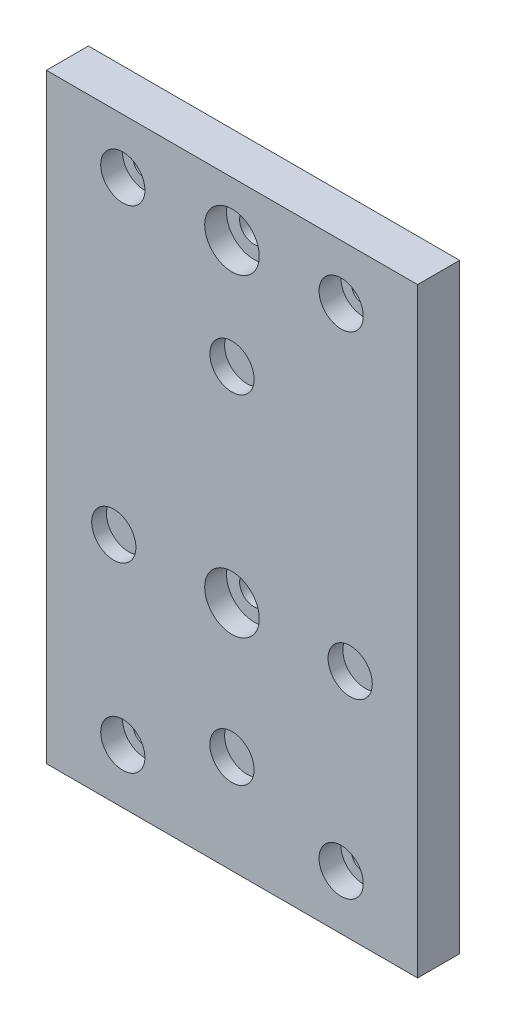
SolidWorks part; units mm, degrees
ref_plane "Front Plane" through (0, 0, 0) normal (0, 0, 1) x (1, 0, 0)
ref_plane "Top Plane" through (0, 0, 0) normal (0, 1, 0) x (1, 0, 0)
ref_plane "Right Plane" through (0, 0, 0) normal (1, 0, 0) x (0, 0, -1)
sketch "Sketch1" plane through (0, 0, 0) normal (0, 0, 1) x (1, 0, 0)
  line L0 (0, -45) -> (0, -41) construction
  line L1 (-34, 55) -> (34, 55)
  line L2 (-34, 55) -> (-34, -55)
  line L3 (-34, -55) -> (34, -55)
  line L4 (34, 55) -> (34, -55)
  line L5 (-34, 55) -> (34, -55) construction
  line L6 (-34, -55) -> (34, 55) construction
  line L7 (-20, 45) -> (20, 45) construction
  line L8 (-20, 45) -> (-20, -45) construction
  line L9 (-20, -45) -> (20, -45) construction
  line L10 (20, 45) -> (20, -45) construction
  line L11 (-20, 45) -> (20, -45) construction
  line L12 (-20, -45) -> (20, 45) construction
  line L13 (0, 25) -> (-21.6506, -12.5) construction
  line L14 (-21.6506, -12.5) -> (21.6506, -12.5) construction
  line L15 (21.6506, -12.5) -> (0, 25) construction
  circle A0 centre (20, 45) radius 2.1
  circle A1 centre (-20, 45) radius 2.1
  circle A2 centre (20, -45) radius 2.1
  circle A3 centre (-20, -45) radius 2.1
  circle A4 centre (0, 0) radius 25 construction
  circle A5 centre (21.6506, -12.5) radius 4.05
  circle A6 centre (0, 25) radius 4.05
  circle A7 centre (-21.6506, -12.5) radius 4.05
  circle A9 centre (0, -36.95) radius 4.05
  circle A10 centre (0, 45) radius 2.6
  circle A11 centre (0, -12.5) radius 2.6
  point P0 (0, 0)
  point P6 (0, 0)
extrude "Boss-Extrude1" add sketch "Sketch1" along normal blind 7.7
sketch "Sketch2" plane through (0, 0, 0) normal (0, 0, -1) x (-1, 0, 0)
  circle A0 centre (-21.6506, -12.5) radius 6.3046
  circle A1 centre (0, 25) radius 7.3343
  circle A2 centre (21.6506, -12.5) radius 8.114
  circle A3 centre (0, -36.95) radius 11.0737
extrude "Boss-Extrude2" add sketch "Sketch2" against normal blind 5
sketch "Sketch3" plane through (0, 0, 7.7) normal (0, 0, -1) x (-1, 0, 0)
  circle A0 centre (-20, 45) radius 4.05
  circle A1 centre (20, 45) radius 4.05
  circle A2 centre (-20, -45) radius 4.05
  circle A3 centre (20, -45) radius 4.05
  circle A4 centre (0, 45) radius 5
  circle A5 centre (0, -12.5) radius 5
extrude "Cut-Extrude1" cut sketch "Sketch3" along normal blind 4
